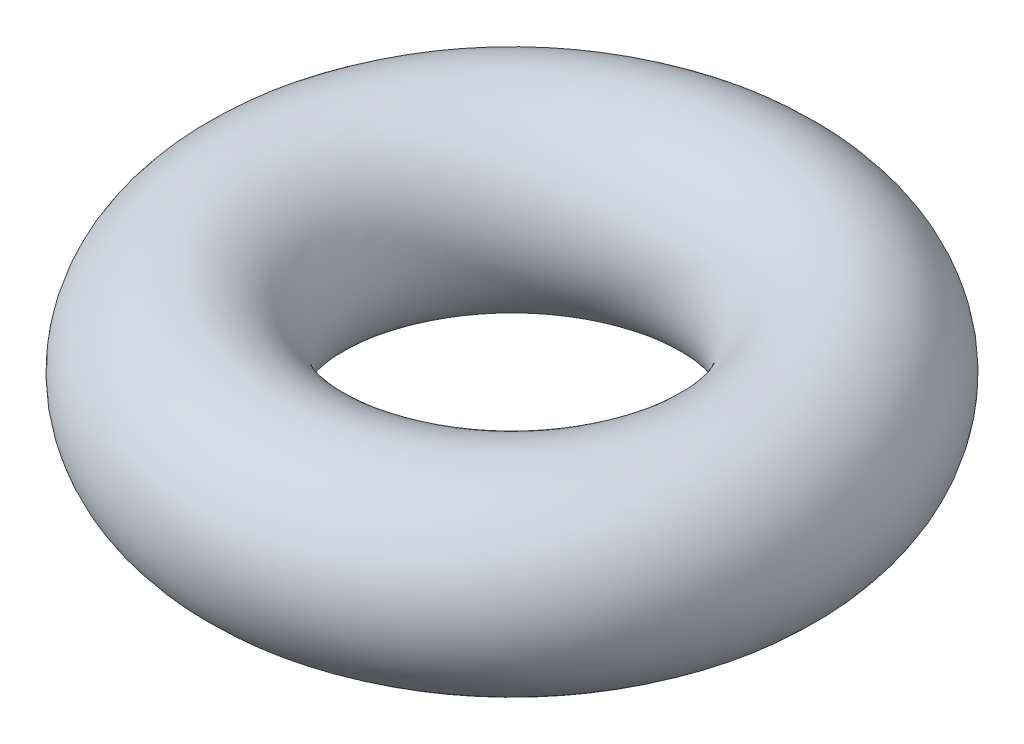
SolidWorks part; units mm, degrees
ref_plane "Alzado" through (0, 0, 0) normal (0, 0, 1) x (1, 0, 0)
ref_plane "Planta" through (0, 0, 0) normal (0, 1, 0) x (1, 0, 0)
ref_plane "Vista lateral" through (0, 0, 0) normal (1, 0, 0) x (0, 0, -1)
sketch "Croquis1" plane through (0, 0, 0) normal (0, 0, 1) x (1, 0, 0)
  line L0 (0, 0) -> (0, 1.919) construction
  circle A0 centre (2.5, 0) radius 1
  dimension "D1" = 2
  dimension "D2" = 2.5
revolve "Revolución1" add sketch "Croquis1" angle 360 about L0
sketch "Croquis2" plane through (0, 0, 0) normal (0, 1, 0) x (1, 0, 0)
  circle A0 centre (0, 0) radius 2.5 construction
  dimension "D1" = 5
